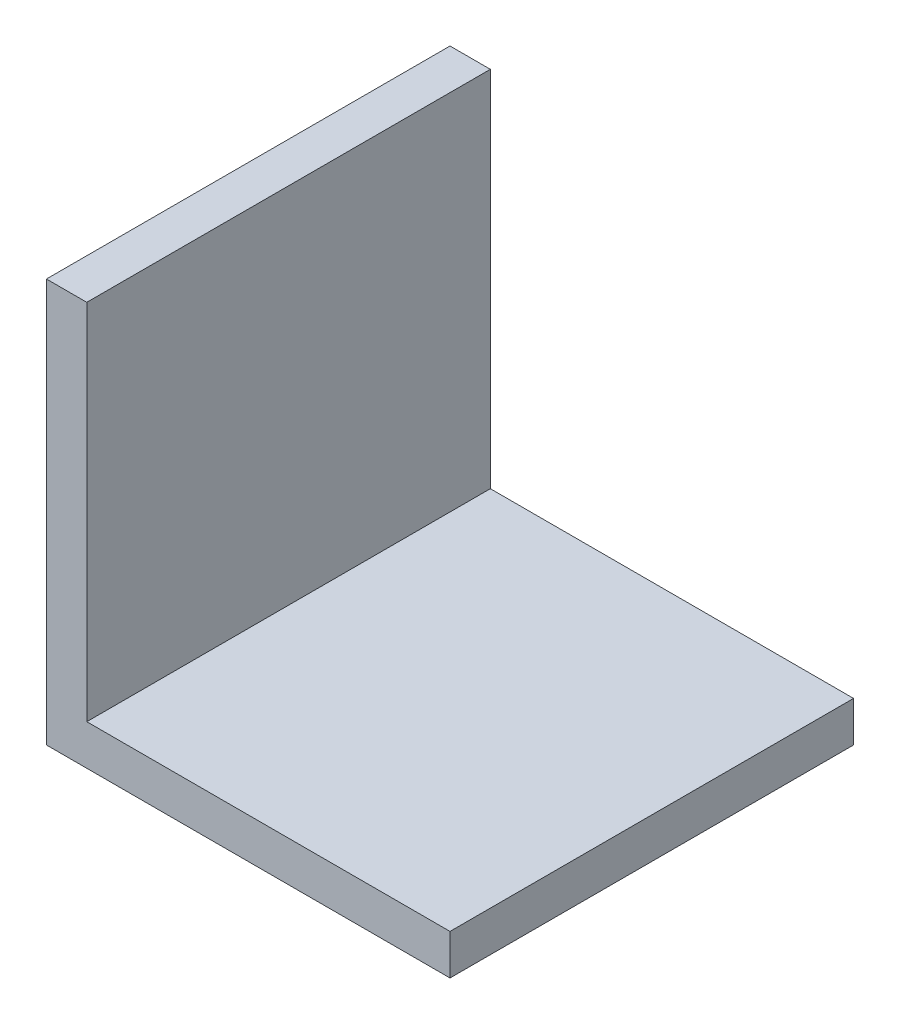
SolidWorks part; units mm, degrees
ref_plane "Front Plane" through (0, 0, 0) normal (0, 0, 1) x (1, 0, 0)
ref_plane "Top Plane" through (0, 0, 0) normal (0, 1, 0) x (1, 0, 0)
ref_plane "Right Plane" through (0, 0, 0) normal (1, 0, 0) x (0, 0, -1)
sketch "Sketch1" plane through (0, 0, 0) normal (0, 1, 0) x (1, 0, 0)
  line L1 (-75.0264, 9.1132) -> (-45.0264, 9.1132)
  line L2 (-75.0264, 9.1132) -> (-75.0264, -20.8868)
  line L3 (-75.0264, -20.8868) -> (-45.0264, -20.8868)
  line L4 (-45.0264, 9.1132) -> (-45.0264, -20.8868)
extrude "Boss-Extrude1" add sketch "Sketch1" along normal blind 30
shell "Shell1" thickness 3
